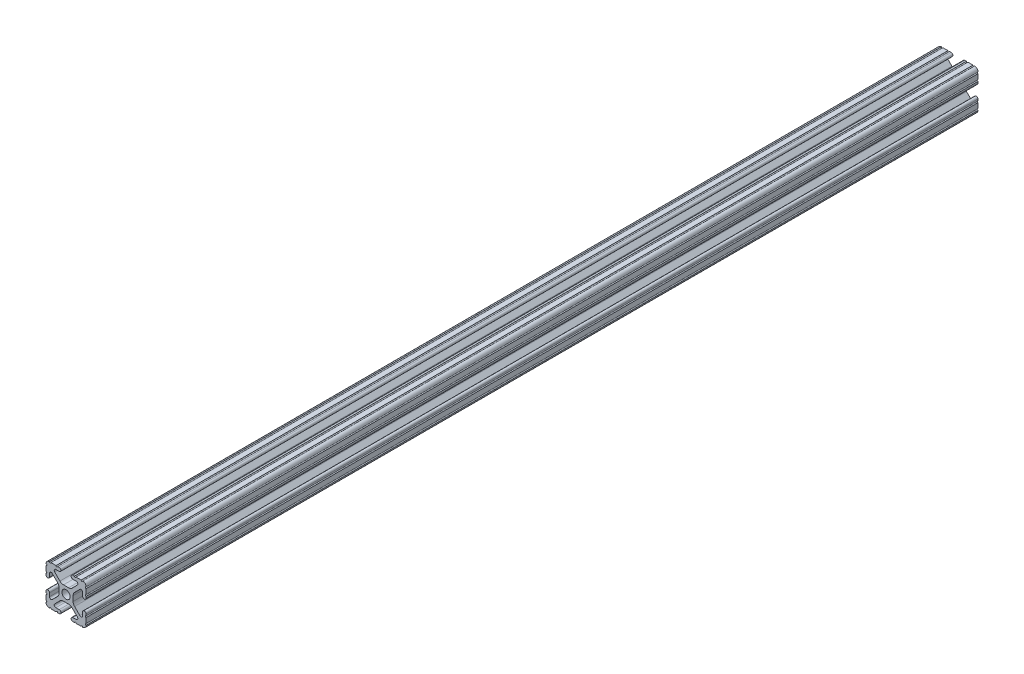
SolidWorks part; units mm, degrees
ref_plane "Front Plane" through (0, 0, 0) normal (0, 0, 1) x (1, 0, 0)
ref_plane "Top Plane" through (0, 0, 0) normal (0, 1, 0) x (1, 0, 0)
ref_plane "Right Plane" through (0, 0, 0) normal (1, 0, 0) x (0, 0, -1)
sketch "Sketch1" plane through (0, 0, 0) normal (0, 0, 1) x (1, 0, 0)
  line L0 (-12.7, -6.3331) -> (-12.7, -9.5504)
  line L1 (-9.5504, -12.7) -> (-6.3331, -12.7)
  line L2 (-5.3171, -12.7) -> (-4.3434, -12.7)
  line L3 (-4.3434, -10.4902) -> (-6.4748, -10.4902)
  line L4 (-7.1932, -8.7558) -> (-3.8632, -5.4257)
  line L5 (-1.6181, -4.4958) -> (1.6181, -4.4958)
  line L6 (3.8632, -5.4257) -> (7.1932, -8.7558)
  line L7 (6.4748, -10.4902) -> (4.3434, -10.4902)
  line L8 (4.3434, -12.7) -> (5.3171, -12.7)
  line L9 (6.3331, -12.7) -> (9.5504, -12.7)
  line L10 (12.7, -9.5504) -> (12.7, -6.3331)
  line L11 (12.7, -5.3171) -> (12.7, -4.3434)
  line L12 (10.4902, -4.3434) -> (10.4902, -6.4748)
  line L13 (8.7558, -7.1932) -> (5.4257, -3.8632)
  line L14 (4.4958, -1.6181) -> (4.4958, 1.6181)
  line L15 (5.4257, 3.8632) -> (8.7558, 7.1932)
  line L16 (10.4902, 6.4748) -> (10.4902, 4.3434)
  line L17 (12.7, 4.3434) -> (12.7, 5.3171)
  line L18 (12.7, 6.3331) -> (12.7, 9.5504)
  line L19 (9.5504, 12.7) -> (6.3331, 12.7)
  line L20 (5.3171, 12.7) -> (4.3434, 12.7)
  line L21 (4.3434, 10.4902) -> (6.4748, 10.4902)
  line L22 (7.1932, 8.7558) -> (3.8632, 5.4257)
  line L23 (1.6181, 4.4958) -> (-1.6181, 4.4958)
  line L24 (-3.8632, 5.4257) -> (-7.1932, 8.7558)
  line L25 (-6.4748, 10.4902) -> (-4.3434, 10.4902)
  line L26 (-4.3434, 12.7) -> (-5.3171, 12.7)
  line L27 (-6.3331, 12.7) -> (-9.5504, 12.7)
  line L28 (-12.7, 9.5504) -> (-12.7, 6.3331)
  line L29 (-12.7, 5.3171) -> (-12.7, 4.3434)
  line L30 (-10.4902, 4.3434) -> (-10.4902, 6.4748)
  line L31 (-8.7558, 7.1932) -> (-5.4257, 3.8632)
  line L32 (-4.4958, 1.6181) -> (-4.4958, -1.6181)
  line L33 (-5.4257, -3.8632) -> (-8.7558, -7.1932)
  line L34 (-10.4902, -6.4748) -> (-10.4902, -4.3434)
  line L35 (-12.7, -4.3434) -> (-12.7, -5.3171)
  circle A0 centre (0, 0) radius 2.6035
  arc A1 (-12.7, -5.3171) -> (-12.7, -6.3331) centre (-12.7, -5.8251) cw
  arc A2 (-12.7, -9.5504) -> (-12.6998, -10.5664) centre (-12.7, -10.0584) cw
  arc A3 (-12.6998, -10.5664) -> (-10.5664, -12.6998) centre (-10.5918, -10.5918) ccw
  arc A4 (-10.5664, -12.6998) -> (-9.5504, -12.7) centre (-10.0584, -12.7) cw
  arc A5 (-6.3331, -12.7) -> (-5.3171, -12.7) centre (-5.8251, -12.7) cw
  arc A6 (-4.3434, -12.7) -> (-4.3434, -10.4902) centre (-4.3434, -11.5951) ccw
  arc A7 (-6.4748, -10.4902) -> (-7.1932, -8.7558) centre (-6.4748, -9.4742) cw
  arc A8 (-3.8632, -5.4257) -> (-1.6181, -4.4958) centre (-1.6181, -7.6708) cw
  arc A9 (1.6181, -4.4958) -> (3.8632, -5.4257) centre (1.6181, -7.6708) cw
  arc A10 (7.1932, -8.7558) -> (6.4748, -10.4902) centre (6.4748, -9.4742) cw
  arc A11 (4.3434, -10.4902) -> (4.3434, -12.7) centre (4.3434, -11.5951) ccw
  arc A12 (5.3171, -12.7) -> (6.3331, -12.7) centre (5.8251, -12.7) cw
  arc A13 (9.5504, -12.7) -> (10.5664, -12.6998) centre (10.0584, -12.7) cw
  arc A14 (10.5664, -12.6998) -> (12.6998, -10.5664) centre (10.5918, -10.5918) ccw
  arc A15 (12.6998, -10.5664) -> (12.7, -9.5504) centre (12.7, -10.0584) cw
  arc A16 (12.7, -6.3331) -> (12.7, -5.3171) centre (12.7, -5.8251) cw
  arc A17 (12.7, -4.3434) -> (10.4902, -4.3434) centre (11.5951, -4.3434) ccw
  arc A18 (10.4902, -6.4748) -> (8.7558, -7.1932) centre (9.4742, -6.4748) cw
  arc A19 (5.4257, -3.8632) -> (4.4958, -1.6181) centre (7.6708, -1.6181) cw
  arc A20 (4.4958, 1.6181) -> (5.4257, 3.8632) centre (7.6708, 1.6181) cw
  arc A21 (8.7558, 7.1932) -> (10.4902, 6.4748) centre (9.4742, 6.4748) cw
  arc A22 (10.4902, 4.3434) -> (12.7, 4.3434) centre (11.5951, 4.3434) ccw
  arc A23 (12.7, 5.3171) -> (12.7, 6.3331) centre (12.7, 5.8251) cw
  arc A24 (12.7, 9.5504) -> (12.6998, 10.5664) centre (12.7, 10.0584) cw
  arc A25 (12.6998, 10.5664) -> (10.5664, 12.6998) centre (10.5918, 10.5918) ccw
  arc A26 (10.5664, 12.6998) -> (9.5504, 12.7) centre (10.0584, 12.7) cw
  arc A27 (6.3331, 12.7) -> (5.3171, 12.7) centre (5.8251, 12.7) cw
  arc A28 (4.3434, 12.7) -> (4.3434, 10.4902) centre (4.3434, 11.5951) ccw
  arc A29 (6.4748, 10.4902) -> (7.1932, 8.7558) centre (6.4748, 9.4742) cw
  arc A30 (3.8632, 5.4257) -> (1.6181, 4.4958) centre (1.6181, 7.6708) cw
  arc A31 (-1.6181, 4.4958) -> (-3.8632, 5.4257) centre (-1.6181, 7.6708) cw
  arc A32 (-7.1932, 8.7558) -> (-6.4748, 10.4902) centre (-6.4748, 9.4742) cw
  arc A33 (-4.3434, 10.4902) -> (-4.3434, 12.7) centre (-4.3434, 11.5951) ccw
  arc A34 (-5.3171, 12.7) -> (-6.3331, 12.7) centre (-5.8251, 12.7) cw
  arc A35 (-9.5504, 12.7) -> (-10.5664, 12.6998) centre (-10.0584, 12.7) cw
  arc A36 (-10.5664, 12.6998) -> (-12.6998, 10.5664) centre (-10.5918, 10.5918) ccw
  arc A37 (-12.6998, 10.5664) -> (-12.7, 9.5504) centre (-12.7, 10.0584) cw
  arc A38 (-12.7, 6.3331) -> (-12.7, 5.3171) centre (-12.7, 5.8251) cw
  arc A39 (-12.7, 4.3434) -> (-10.4902, 4.3434) centre (-11.5951, 4.3434) ccw
  arc A40 (-10.4902, 6.4748) -> (-8.7558, 7.1932) centre (-9.4742, 6.4748) cw
  arc A41 (-5.4257, 3.8632) -> (-4.4958, 1.6181) centre (-7.6708, 1.6181) cw
  arc A42 (-4.4958, -1.6181) -> (-5.4257, -3.8632) centre (-7.6708, -1.6181) cw
  arc A43 (-8.7558, -7.1932) -> (-10.4902, -6.4748) centre (-9.4742, -6.4748) cw
  arc A44 (-10.4902, -4.3434) -> (-12.7, -4.3434) centre (-11.5951, -4.3434) ccw
extrude "Boss-Extrude1" add sketch "Sketch1" against normal blind 565.15
